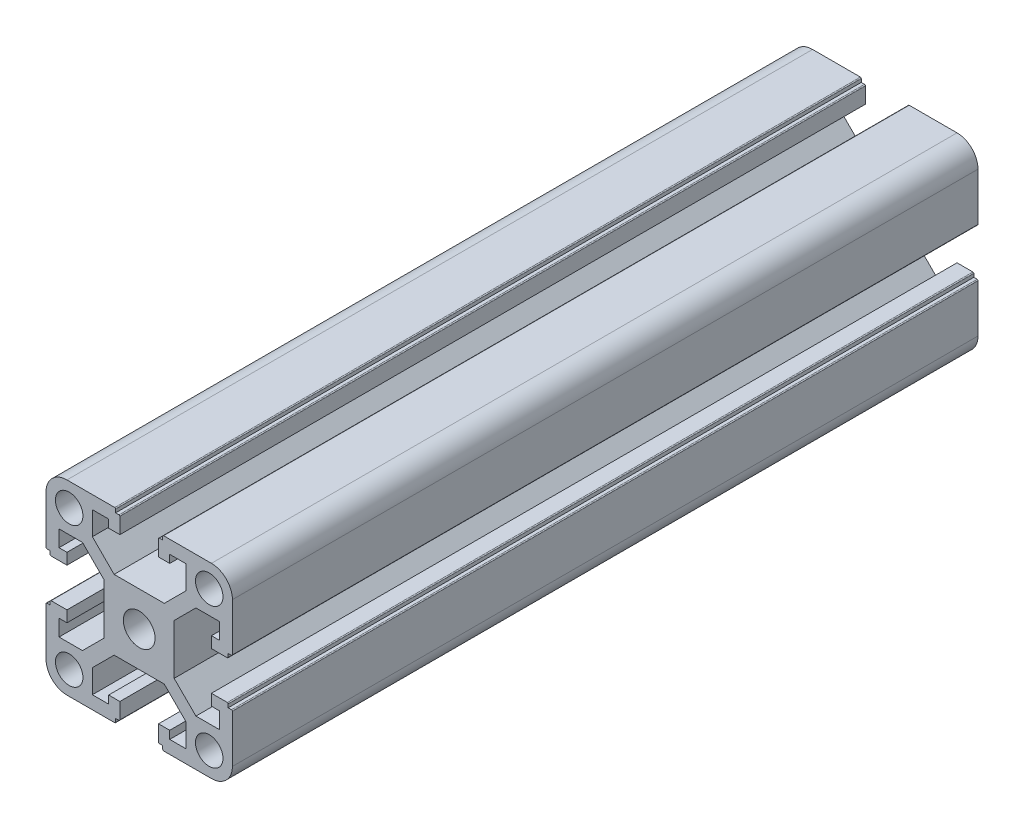
SolidWorks part; units mm, degrees
material "6061-T6 (SS)"
ref_plane "前视基准面" through (0, 0, 0) normal (0, 0, 1) x (1, 0, 0)
ref_plane "上视基准面" through (0, 0, 0) normal (0, 1, 0) x (1, 0, 0)
ref_plane "右视基准面" through (0, 0, 0) normal (1, 0, 0) x (0, 0, -1)
ref_plane "基准面1" through (0, 0, 50) normal (0, 0, 1) x (1, 0, 0)
sketch "草图1" plane through (0, 0, 50) normal (0, 0, 1) x (1, 0, 0)
  line L0 (-1518.245, 3588.0043) -> (-1518.245, 3582.9756)
  line L1 (-1518.245, 3582.9756) -> (-1522.9163, 3578.3043)
  line L2 (-1522.9163, 3578.3043) -> (-1533.6737, 3578.3043)
  line L3 (-1533.6737, 3578.3043) -> (-1538.345, 3582.9756)
  line L4 (-1538.345, 3582.9756) -> (-1538.345, 3588.0043)
  line L5 (-1538.345, 3588.0043) -> (-1534.845, 3588.0043)
  line L6 (-1534.845, 3588.0043) -> (-1534.845, 3586.3043)
  line L7 (-1534.845, 3586.3043) -> (-1532.445, 3586.3043)
  line L8 (-1532.445, 3586.3043) -> (-1532.445, 3589.7043)
  line L9 (-1532.645, 3589.9043) -> (-1533.345, 3589.9043)
  line L10 (-1533.345, 3589.9043) -> (-1533.345, 3590.6043)
  line L11 (-1533.545, 3590.8043) -> (-1543.795, 3590.8043)
  line L12 (-1548.295, 3586.3043) -> (-1548.295, 3576.0543)
  line L13 (-1548.095, 3575.8543) -> (-1547.395, 3575.8543)
  line L14 (-1547.395, 3575.8543) -> (-1547.395, 3575.1543)
  line L15 (-1547.195, 3574.9543) -> (-1543.795, 3574.9543)
  line L16 (-1543.795, 3574.9543) -> (-1543.795, 3577.3543)
  line L17 (-1543.795, 3577.3543) -> (-1545.495, 3577.3543)
  line L18 (-1545.495, 3577.3543) -> (-1545.495, 3580.8543)
  line L19 (-1545.495, 3580.8543) -> (-1540.4663, 3580.8543)
  line L20 (-1540.4663, 3580.8543) -> (-1535.795, 3576.183)
  line L21 (-1535.795, 3576.183) -> (-1535.795, 3565.4256)
  line L22 (-1535.795, 3565.4256) -> (-1540.4663, 3560.7543)
  line L23 (-1540.4663, 3560.7543) -> (-1545.495, 3560.7543)
  line L24 (-1545.495, 3560.7543) -> (-1545.495, 3564.2543)
  line L25 (-1545.495, 3564.2543) -> (-1543.795, 3564.2543)
  line L26 (-1543.795, 3564.2543) -> (-1543.795, 3566.6543)
  line L27 (-1543.795, 3566.6543) -> (-1547.195, 3566.6543)
  line L28 (-1547.395, 3566.4543) -> (-1547.395, 3565.7543)
  line L29 (-1547.395, 3565.7543) -> (-1548.095, 3565.7543)
  line L30 (-1548.295, 3565.5543) -> (-1548.295, 3555.3043)
  line L31 (-1543.795, 3550.8043) -> (-1533.545, 3550.8043)
  line L32 (-1533.345, 3551.0043) -> (-1533.345, 3551.7043)
  line L33 (-1533.345, 3551.7043) -> (-1532.645, 3551.7043)
  line L34 (-1532.445, 3551.9043) -> (-1532.445, 3555.3043)
  line L35 (-1532.445, 3555.3043) -> (-1534.845, 3555.3043)
  line L36 (-1534.845, 3555.3043) -> (-1534.845, 3553.6043)
  line L37 (-1534.845, 3553.6043) -> (-1538.345, 3553.6043)
  line L38 (-1538.345, 3553.6043) -> (-1538.345, 3558.633)
  line L39 (-1538.345, 3558.633) -> (-1533.6737, 3563.3043)
  line L40 (-1533.6737, 3563.3043) -> (-1522.9163, 3563.3043)
  line L41 (-1522.9163, 3563.3043) -> (-1518.245, 3558.633)
  line L42 (-1518.245, 3558.633) -> (-1518.245, 3553.6043)
  line L43 (-1518.245, 3553.6043) -> (-1521.745, 3553.6043)
  line L44 (-1521.745, 3553.6043) -> (-1521.745, 3555.3043)
  line L45 (-1521.745, 3555.3043) -> (-1524.145, 3555.3043)
  line L46 (-1524.145, 3555.3043) -> (-1524.145, 3551.9043)
  line L47 (-1523.945, 3551.7043) -> (-1523.245, 3551.7043)
  line L48 (-1523.245, 3551.7043) -> (-1523.245, 3551.0043)
  line L49 (-1523.045, 3550.8043) -> (-1512.795, 3550.8043)
  line L50 (-1508.295, 3555.3043) -> (-1508.295, 3565.5543)
  line L51 (-1508.495, 3565.7543) -> (-1509.195, 3565.7543)
  line L52 (-1509.195, 3565.7543) -> (-1509.195, 3566.4543)
  line L53 (-1509.395, 3566.6543) -> (-1512.795, 3566.6543)
  line L54 (-1512.795, 3566.6543) -> (-1512.795, 3564.2543)
  line L55 (-1512.795, 3564.2543) -> (-1511.095, 3564.2543)
  line L56 (-1511.095, 3564.2543) -> (-1511.095, 3560.7543)
  line L57 (-1511.095, 3560.7543) -> (-1516.1237, 3560.7543)
  line L58 (-1516.1237, 3560.7543) -> (-1520.795, 3565.4256)
  line L59 (-1520.795, 3565.4256) -> (-1520.795, 3576.183)
  line L60 (-1520.795, 3576.183) -> (-1516.1237, 3580.8543)
  line L61 (-1516.1237, 3580.8543) -> (-1511.095, 3580.8543)
  line L62 (-1511.095, 3580.8543) -> (-1511.095, 3577.3543)
  line L63 (-1511.095, 3577.3543) -> (-1512.795, 3577.3543)
  line L64 (-1512.795, 3577.3543) -> (-1512.795, 3574.9543)
  line L65 (-1512.795, 3574.9543) -> (-1509.395, 3574.9543)
  line L66 (-1509.195, 3575.1543) -> (-1509.195, 3575.8543)
  line L67 (-1509.195, 3575.8543) -> (-1508.495, 3575.8543)
  line L68 (-1508.295, 3576.0543) -> (-1508.295, 3586.3043)
  line L69 (-1512.795, 3590.8043) -> (-1523.045, 3590.8043)
  line L70 (-1523.245, 3590.6043) -> (-1523.245, 3589.9043)
  line L71 (-1523.245, 3589.9043) -> (-1523.945, 3589.9043)
  line L72 (-1524.145, 3589.7043) -> (-1524.145, 3586.3043)
  line L73 (-1524.145, 3586.3043) -> (-1521.745, 3586.3043)
  line L74 (-1521.745, 3586.3043) -> (-1521.745, 3588.0043)
  line L75 (-1521.745, 3588.0043) -> (-1518.245, 3588.0043)
  circle A0 centre (-1513.27, 3555.7793) radius 2.95
  circle A1 centre (-1528.295, 3570.8043) radius 3.4
  circle A2 centre (-1513.27, 3585.8293) radius 2.95
  arc A3 (-1532.445, 3589.7043) -> (-1532.645, 3589.9043) centre (-1532.645, 3589.7043) ccw
  arc A4 (-1533.345, 3590.6043) -> (-1533.545, 3590.8043) centre (-1533.545, 3590.6043) ccw
  arc A5 (-1543.795, 3590.8043) -> (-1548.295, 3586.3043) centre (-1543.795, 3586.3043) ccw
  arc A6 (-1548.295, 3576.0543) -> (-1548.095, 3575.8543) centre (-1548.095, 3576.0543) ccw
  arc A7 (-1547.395, 3575.1543) -> (-1547.195, 3574.9543) centre (-1547.195, 3575.1543) ccw
  arc A8 (-1547.195, 3566.6543) -> (-1547.395, 3566.4543) centre (-1547.195, 3566.4543) ccw
  arc A9 (-1548.095, 3565.7543) -> (-1548.295, 3565.5543) centre (-1548.095, 3565.5543) ccw
  arc A10 (-1548.295, 3555.3043) -> (-1543.795, 3550.8043) centre (-1543.795, 3555.3043) ccw
  arc A11 (-1533.545, 3550.8043) -> (-1533.345, 3551.0043) centre (-1533.545, 3551.0043) ccw
  arc A12 (-1532.645, 3551.7043) -> (-1532.445, 3551.9043) centre (-1532.645, 3551.9043) ccw
  arc A13 (-1524.145, 3551.9043) -> (-1523.945, 3551.7043) centre (-1523.945, 3551.9043) ccw
  arc A14 (-1523.245, 3551.0043) -> (-1523.045, 3550.8043) centre (-1523.045, 3551.0043) ccw
  arc A15 (-1512.795, 3550.8043) -> (-1508.295, 3555.3043) centre (-1512.795, 3555.3043) ccw
  arc A16 (-1508.295, 3565.5543) -> (-1508.495, 3565.7543) centre (-1508.495, 3565.5543) ccw
  arc A17 (-1509.195, 3566.4543) -> (-1509.395, 3566.6543) centre (-1509.395, 3566.4543) ccw
  arc A18 (-1509.395, 3574.9543) -> (-1509.195, 3575.1543) centre (-1509.395, 3575.1543) ccw
  arc A19 (-1508.495, 3575.8543) -> (-1508.295, 3576.0543) centre (-1508.495, 3576.0543) ccw
  arc A20 (-1508.295, 3586.3043) -> (-1512.795, 3590.8043) centre (-1512.795, 3586.3043) ccw
  arc A21 (-1523.045, 3590.8043) -> (-1523.245, 3590.6043) centre (-1523.045, 3590.6043) ccw
  arc A22 (-1523.945, 3589.9043) -> (-1524.145, 3589.7043) centre (-1523.945, 3589.7043) ccw
  circle A23 centre (-1543.32, 3585.8293) radius 2.95
  circle A24 centre (-1543.32, 3555.7793) radius 2.95
extrude "凸台-拉伸1" add sketch "草图1" against normal mid plane 160
ref_plane "基准面2" through (-1528.295, 0, 0) normal (1, 0, 0) x (0, 0, -1)
ref_plane "基准面3" through (0, 3570.8043, 0) normal (0, 1, 0) x (1, 0, 0)
